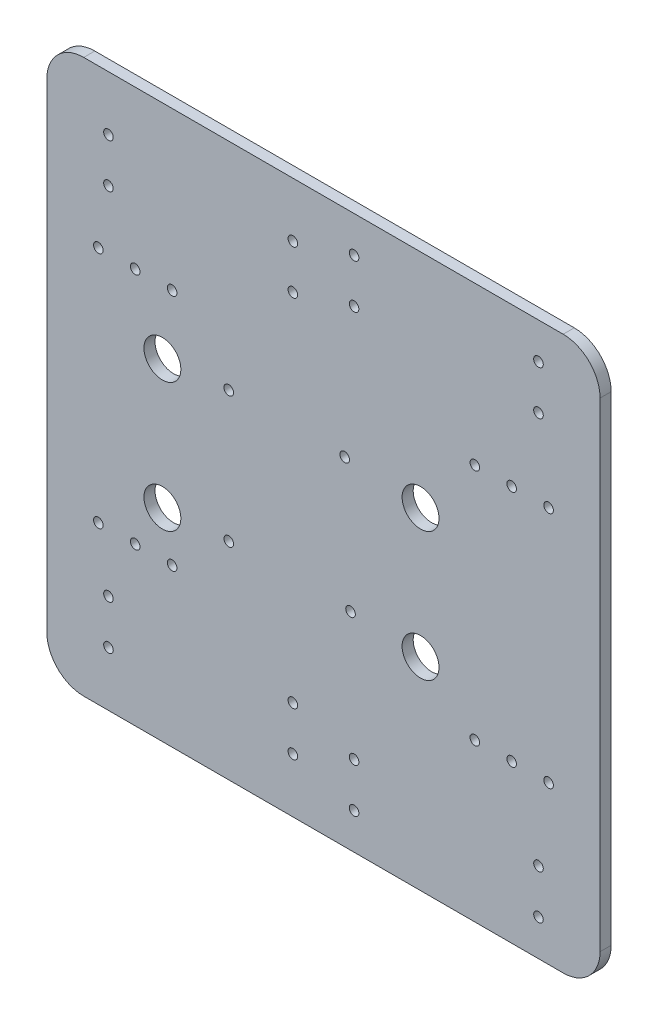
SolidWorks part; units mm, degrees
ref_plane "前视基准面" through (0, 0, 0) normal (0, 0, 1) x (1, 0, 0)
ref_plane "上视基准面" through (0, 0, 0) normal (0, 1, 0) x (1, 0, 0)
ref_plane "右视基准面" through (0, 0, 0) normal (1, 0, 0) x (0, 0, -1)
sketch "草图1" plane through (0, 0, 0) normal (0, 0, 1) x (1, 0, 0)
  line L0 (18.2125, -70.45) -> (10.2234, -70.45) construction
  line L1 (-65, -75) -> (65, -75)
  line L2 (-75, -65) -> (-75, 65)
  line L3 (-65, 75) -> (65, 75)
  line L4 (75, -65) -> (75, 65)
  line L5 (-75, -75) -> (75, 75) construction
  line L6 (-75, 75) -> (75, -75) construction
  line L7 (9.1, -70.45) -> (14.5, -70.45) construction
  line L8 (58.1843, -70.45) -> (64.6962, -70.45) construction
  line L9 (52.1, -70.45) -> (57.5, -70.45) construction
  arc A0 (-75, -65) -> (-65, -75) centre (-65, -65) ccw
  arc A1 (-65, 75) -> (-75, 65) centre (-65, 65) ccw
  arc A2 (65, -75) -> (75, -65) centre (65, -65) ccw
  arc A3 (65, 75) -> (75, 65) centre (65, 65) cw
  point P0 (0, 0)
  dimension "D2" = 10
  dimension "D3" = 10
  dimension "D1" = 150
extrude "凸台-拉伸1" add sketch "草图1" along normal blind 3
sketch "草图2" plane through (0, 0, 0) normal (0, 0, -1) x (-1, 0, 0)
  line L9 (-28, -30) -> (28, -30)
  line L10 (-28, -30) -> (-28, 30)
  line L11 (-28, 30) -> (28, 30)
  line L12 (28, -30) -> (28, 30)
  line L13 (-28, -30) -> (28, 30) construction
  line L14 (-28, 30) -> (28, -30) construction
  point P0 (0, 0)
  point P1 (0, 0)
  point P2 (0, 0)
  dimension "D1" = 60
  dimension "D2" = 56
sketch "草图4" plane through (0, 0, 0) normal (0, 0, -1) x (-1, 0, 0)
  line L0 (-65, 75) -> (-65, -75) construction
  line L1 (65, 75) -> (65, 65.45) construction
  line L7 (0, 0) -> (0, 47.2726) construction
  line L24 (0, 0) -> (51.5142, 0) construction
  line L51 (65, 59.45) -> (65, -75) construction
  arc A0 (75, 65) -> (65, 75) centre (65, 65) ccw construction
sketch "草图8" plane through (0, 0, 0) normal (0, 0, -1) x (-1, 0, 0)
  line L0 (0, 75) -> (0, 17.0391) construction
  line L1 (-65, 75) -> (65, 75) construction
  line L2 (0, 0) -> (0, 47.2726) construction
  line L3 (75, 0) -> (-28.7423, 0) construction
  line L4 (75, 65) -> (75, -65) construction
  line L5 (0, -75) -> (0, -17.0391) construction
  circle A0 centre (58.3, 60.2) radius 1.3 construction
  circle A1 centre (58.3, 48.2) radius 1.3 construction
  circle A4 centre (8.3, 60.2) radius 1.3
  circle A5 centre (8.3, 48.2) radius 1.3
  circle A10 centre (8.3, -48.2) radius 1.3
  circle A11 centre (8.3, -60.2) radius 1.3
  circle A12 centre (58.3, -48.2) radius 1.3
  circle A13 centre (58.3, -60.2) radius 1.3
  circle A18 centre (58.3, 60.2) radius 1.3
  circle A19 centre (58.3, 48.2) radius 1.3
  circle A20 centre (-58.3, 65.2) radius 1.3
  circle A21 centre (-58.3, 53.2) radius 1.3
  circle A22 centre (-8.3, 53.2) radius 1.3
  circle A23 centre (-8.3, 65.2) radius 1.3
  circle A24 centre (-8.3, -65.2) radius 1.3
  circle A25 centre (-8.3, -53.2) radius 1.3
  circle A26 centre (-58.3, -53.2) radius 1.3
  circle A27 centre (-58.3, -65.2) radius 1.3
  dimension "D1" = 2
extrude "切除-拉伸3" cut sketch "草图8" against normal up to surface (3 mm away) up to face at (0, 0, 3)
sketch "草图15" plane through (0, 0, 0) normal (0, 0, -1) x (-1, 0, 0)
  line L0 (0, 75) -> (0, -68.0196) construction
  line L1 (-65, 75) -> (65, 75) construction
  line L2 (75, 0) -> (-92.9415, 0) construction
  line L3 (75, 65) -> (75, -65) construction
  circle A26 centre (-5.7647, 16.5426) radius 1.3
  circle A27 centre (25.6806, 16.5426) radius 1.3
  circle A28 centre (25.6806, -18.9667) radius 1.3
  circle A29 centre (-7.3395, -18.9667) radius 1.3
  circle A30 centre (43.674, 14.905) radius 5
  circle A31 centre (43.674, -20.095) radius 5
  circle A32 centre (-26.326, 14.905) radius 5
  circle A33 centre (-26.326, -20.095) radius 5
  circle A34 centre (-51.0383, 32.2875) radius 1.3
  circle A35 centre (51.0383, 32.2875) radius 1.3
  circle A36 centre (51.0383, -32.2875) radius 1.3
  circle A37 centre (-51.0383, -32.2875) radius 1.3
  circle A38 centre (-41.0383, 32.2875) radius 1.3
  circle A39 centre (61.0383, 32.2875) radius 1.3
  circle A40 centre (61.0383, -32.2875) radius 1.3
  circle A41 centre (-41.0383, -32.2875) radius 1.3
  circle A42 centre (-61.0383, -32.2875) radius 1.3
  circle A43 centre (41.0383, -32.2875) radius 1.3
  circle A44 centre (41.0383, 32.2875) radius 1.3
  circle A45 centre (-61.0383, 32.2875) radius 1.3
  dimension "D2" = 2.6
  dimension "D3" = 2.6
  dimension "D4" = 2
  dimension "D5" = 2.6
  dimension "D1" = 10
  dimension "D7" = 2.6
  dimension "D8" = 2
  dimension "D6" = 2
  dimension "D9" = 2
extrude "切除-拉伸7" cut sketch "草图15" against normal up to next
